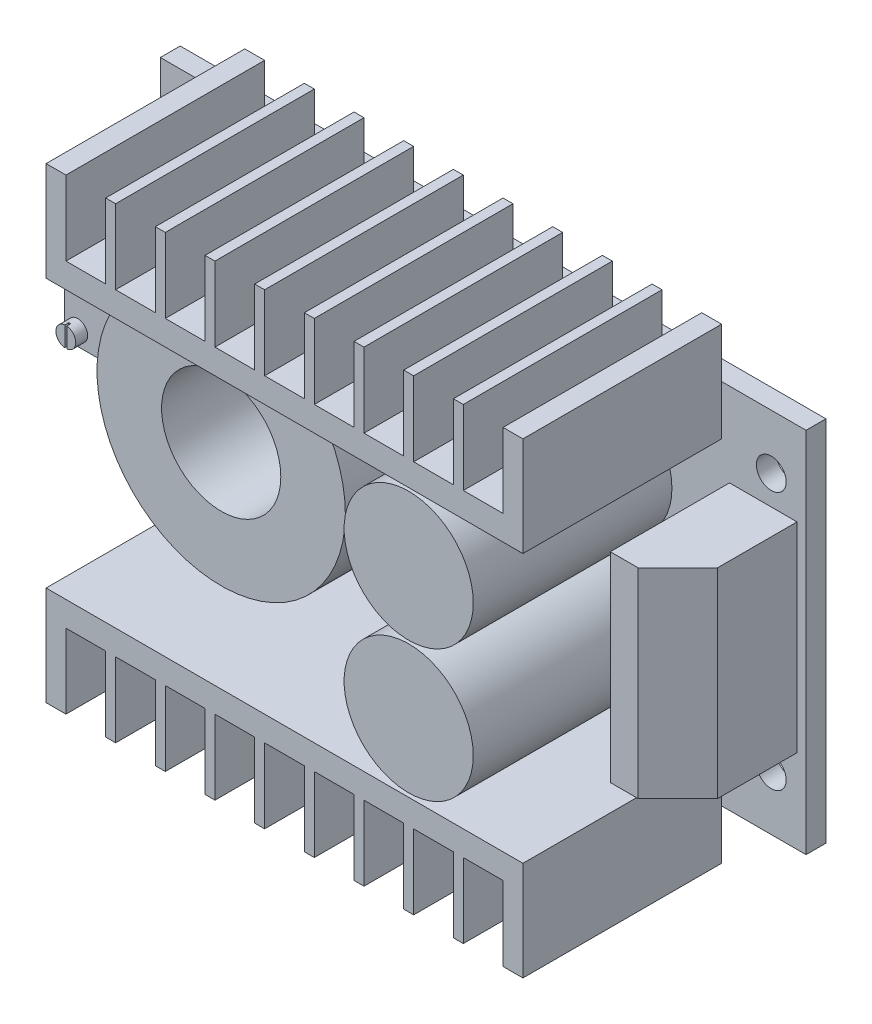
SolidWorks part; units mm, degrees
ref_plane "Front" through (0, 0, 0) normal (0, 0, 1) x (1, 0, 0)
ref_plane "Top" through (0, 0, 0) normal (0, 1, 0) x (1, 0, 0)
ref_plane "Right" through (0, 0, 0) normal (1, 0, 0) x (0, 0, -1)
sketch "Эскиз1" plane through (0, 0, 0) normal (0, 0, 1) x (1, 0, 0)
  line L1 (-32.5, 18.5) -> (32.5, 18.5)
  line L2 (-32.5, 18.5) -> (-32.5, -18.5)
  line L3 (-32.5, -18.5) -> (32.5, -18.5)
  line L4 (32.5, 18.5) -> (32.5, -18.5)
  line L5 (0, -18.5) -> (0, 18.5) construction
  line L6 (-32.5, 0) -> (32.5, 0) construction
  point P0 (0, 0)
  dimension "D1" = 37
  dimension "D2" = 65
extrude "Бобышка-Вытянуть1" add sketch "Эскиз1" along normal blind 2
sketch "Эскиз2" plane through (0, 0, 2) normal (0, 0, 1) x (1, 0, 0)
  line L0 (32.5, 18.5) -> (-32.5, 18.5) construction
  line L1 (-24, 23.5) -> (24, 23.5) construction
  line L2 (-24, 23.5) -> (-24, 13.5)
  line L3 (-24, 13.5) -> (24, 13.5)
  line L4 (24, 23.5) -> (24, 13.5)
  line L5 (0, 13.5) -> (0, 23.5) construction
  line L6 (-24, 18.5) -> (24, 18.5) construction
  line L7 (-22, 23.5) -> (-24, 23.5)
  line L8 (-2, 16) -> (2, 16)
  line L9 (-2, 16) -> (-2, 23.5)
  line L11 (2, 16) -> (2, 23.5)
  line L12 (0, 23.5) -> (0, 16) construction
  line L13 (-2, 19.75) -> (2, 19.75) construction
  line L14 (-3, 23.5) -> (-2, 23.5)
  line L15 (-3, 16) -> (-3, 23.5)
  line L16 (-7, 16) -> (-3, 16)
  line L17 (-7, 16) -> (-7, 23.5)
  line L18 (-8, 23.5) -> (-7, 23.5)
  line L19 (-8, 16) -> (-8, 23.5)
  line L20 (-12, 16) -> (-8, 16)
  line L21 (-12, 16) -> (-12, 23.5)
  line L22 (-13, 23.5) -> (-12, 23.5)
  line L23 (-13, 16) -> (-13, 23.5)
  line L24 (-17, 16) -> (-13, 16)
  line L25 (-17, 16) -> (-17, 23.5)
  line L26 (-18, 23.5) -> (-17, 23.5)
  line L27 (-18, 16) -> (-18, 23.5)
  line L28 (-22, 16) -> (-18, 16)
  line L29 (-22, 16) -> (-22, 23.5)
  line L30 (2, 23.5) -> (3, 23.5)
  line L31 (3, 16) -> (3, 23.5)
  line L32 (3, 16) -> (7, 16)
  line L33 (7, 16) -> (7, 23.5)
  line L34 (7, 23.5) -> (8, 23.5)
  line L35 (8, 16) -> (8, 23.5)
  line L36 (8, 16) -> (12, 16)
  line L37 (12, 16) -> (12, 23.5)
  line L38 (12, 23.5) -> (13, 23.5)
  line L39 (13, 16) -> (13, 23.5)
  line L40 (13, 16) -> (17, 16)
  line L41 (17, 16) -> (17, 23.5)
  line L42 (17, 23.5) -> (18, 23.5)
  line L43 (18, 16) -> (18, 23.5)
  line L44 (18, 16) -> (22, 16)
  line L45 (22, 16) -> (22, 23.5)
  line L46 (22, 23.5) -> (24, 23.5)
  line L47 (-32.5, 0) -> (32.5, 0) construction
  line L48 (-32.5, 18.5) -> (-32.5, -18.5) construction
  line L49 (32.5, -18.5) -> (32.5, 18.5) construction
  line L50 (-2, -19.75) -> (2, -19.75) construction
  line L51 (0, -23.5) -> (0, -16) construction
  line L52 (-24, -18.5) -> (24, -18.5) construction
  line L53 (0, -13.5) -> (0, -23.5) construction
  line L54 (-24, -23.5) -> (24, -23.5) construction
  line L55 (22, -23.5) -> (24, -23.5)
  line L56 (22, -16) -> (22, -23.5)
  line L57 (18, -16) -> (22, -16)
  line L58 (18, -16) -> (18, -23.5)
  line L59 (17, -23.5) -> (18, -23.5)
  line L60 (17, -16) -> (17, -23.5)
  line L61 (13, -16) -> (17, -16)
  line L62 (13, -16) -> (13, -23.5)
  line L63 (12, -23.5) -> (13, -23.5)
  line L64 (12, -16) -> (12, -23.5)
  line L65 (8, -16) -> (12, -16)
  line L66 (8, -16) -> (8, -23.5)
  line L67 (7, -23.5) -> (8, -23.5)
  line L68 (7, -16) -> (7, -23.5)
  line L69 (3, -16) -> (7, -16)
  line L70 (3, -16) -> (3, -23.5)
  line L71 (2, -23.5) -> (3, -23.5)
  line L72 (-22, -16) -> (-22, -23.5)
  line L73 (-22, -16) -> (-18, -16)
  line L74 (-18, -16) -> (-18, -23.5)
  line L75 (-18, -23.5) -> (-17, -23.5)
  line L76 (-17, -16) -> (-17, -23.5)
  line L77 (-17, -16) -> (-13, -16)
  line L78 (-13, -16) -> (-13, -23.5)
  line L79 (-13, -23.5) -> (-12, -23.5)
  line L80 (-12, -16) -> (-12, -23.5)
  line L81 (-12, -16) -> (-8, -16)
  line L82 (-8, -16) -> (-8, -23.5)
  line L83 (-8, -23.5) -> (-7, -23.5)
  line L84 (-7, -16) -> (-7, -23.5)
  line L85 (-7, -16) -> (-3, -16)
  line L86 (-3, -16) -> (-3, -23.5)
  line L87 (-3, -23.5) -> (-2, -23.5)
  line L88 (2, -16) -> (2, -23.5)
  line L89 (-2, -16) -> (-2, -23.5)
  line L90 (-2, -16) -> (2, -16)
  line L91 (-22, -23.5) -> (-24, -23.5)
  line L92 (24, -23.5) -> (24, -13.5)
  line L93 (-24, -13.5) -> (24, -13.5)
  line L94 (-24, -23.5) -> (-24, -13.5)
  point P0 (0, 18.5)
  point P6 (0, 19.75)
  point P103 (0, -19.75)
  point P104 (0, -18.5)
  dimension "D1" = 10
  dimension "D2" = 48
  dimension "D3" = 7.5
  dimension "D4" = 4
  dimension "D5" = 5
  dimension "D6" = 5
extrude "Бобышка-Вытянуть2" add sketch "Эскиз2" along normal blind 20
sketch "Эскиз3" plane through (0, 0, 2) normal (0, 0, 1) x (1, 0, 0)
  line L0 (12.5, 23.5) -> (12.5, -23.5) construction
  line L1 (13, 23.5) -> (12, 23.5) construction
  line L2 (12, -23.5) -> (13, -23.5) construction
  circle A0 centre (12.5, 6.6916) radius 6.5
  circle A1 centre (12.5, -6.6124) radius 6.5
  dimension "D1" = 13
  dimension "D2" = 13
extrude "Бобышка-Вытянуть3" add sketch "Эскиз3" along normal blind 20
sketch "Эскиз4" plane through (0, 0, 2) normal (0, 0, 1) x (1, 0, 0)
  circle A0 centre (-14.3735, 0) radius 12.5
  circle A1 centre (-14.3735, 0) radius 6
  dimension "D1" = 25
  dimension "D2" = 12
extrude "Бобышка-Вытянуть4" add sketch "Эскиз4" along normal blind 12
sketch "Эскиз5" plane through (0, 0, 2) normal (0, 0, 1) x (1, 0, 0)
  line L1 (-32.1494, 9.1427) -> (-27.1494, 9.1427)
  line L2 (-32.1494, 9.1427) -> (-32.1494, -0.8573)
  line L3 (-32.1494, -0.8573) -> (-27.1494, -0.8573)
  line L4 (-27.1494, 9.1427) -> (-27.1494, -0.8573)
  line L5 (-29.6494, -0.8573) -> (-29.6494, 9.1427) construction
  line L6 (-32.1494, 4.1427) -> (-27.1494, 4.1427) construction
  point P0 (-29.6494, 4.1427)
  dimension "D1" = 10
  dimension "D2" = 5
extrude "Бобышка-Вытянуть5" add sketch "Эскиз5" along normal blind 10
sketch "Эскиз6" plane through (0, 0, 12) normal (0, 0, 1) x (1, 0, 0)
  circle A0 centre (-30.8135, 0.582) radius 1
  dimension "D1" = 2
extrude "Бобышка-Вытянуть6" add sketch "Эскиз6" along normal blind 1.2
sketch "Эскиз7" plane through (0, 0, 2) normal (0, 0, 1) x (1, 0, 0)
  line L1 (24.796, 10.0615) -> (31.5947, 10.0615)
  line L2 (24.796, 10.0615) -> (24.796, -10.0615)
  line L3 (24.796, -10.0615) -> (31.5947, -10.0615)
  line L4 (31.5947, 10.0615) -> (31.5947, -10.0615)
  line L5 (28.1954, -10.0615) -> (28.1954, 10.0615) construction
  line L6 (24.796, 0) -> (31.5947, 0) construction
  point P0 (28.1954, 0)
  dimension "D1" = 20.1231
  dimension "D2" = 6.7987
extrude "Бобышка-Вытянуть7" add sketch "Эскиз7" along normal blind 12
chamfer "Фаска1" distance 4 angle 45 1 edges at (31.5947, 0, 14)
sketch "Эскиз8" plane through (0, 0, 2) normal (0, 0, 1) x (1, 0, 0)
  line L1 (-29, 13) -> (29, 13) construction
  line L2 (-29, 13) -> (-29, -13) construction
  line L3 (-29, -13) -> (29, -13) construction
  line L4 (29, 13) -> (29, -13) construction
  line L5 (0, -13) -> (0, 13) construction
  line L6 (-29, 0) -> (29, 0) construction
  circle A0 centre (-29, 13) radius 1.5
  circle A1 centre (29, 13) radius 1.5
  circle A2 centre (29, -13) radius 1.5
  circle A3 centre (-29, -13) radius 1.5
  point P0 (0, 0)
  dimension "D3" = 3
  dimension "D4" = 3
  dimension "D5" = 3
  dimension "D6" = 3
  dimension "D1" = 26
  dimension "D2" = 58
extrude "Вырез-Вытянуть1" cut sketch "Эскиз8" against normal through all
sketch "Sketch1" plane through (0, 0, 13.2) normal (0, 0, 1) x (1, 0, 0)
  line L1 (-30.9135, 1.6192) -> (-30.7135, 1.6192)
  line L2 (-30.9135, 1.6192) -> (-30.9135, -0.6078)
  line L3 (-30.9135, -0.6078) -> (-30.7135, -0.6078)
  line L4 (-30.7135, 1.6192) -> (-30.7135, -0.6078)
  line L5 (-30.9135, 1.6192) -> (-30.7135, -0.6078) construction
  line L6 (-30.9135, -0.6078) -> (-30.7135, 1.6192) construction
  circle A0 centre (-30.8135, 0.582) radius 1 construction
  point P4 (-30.8135, 0.5057)
  dimension "D1" = 0.2
  dimension "D2" = 0.1
extrude "Cut-Extrude1" cut sketch "Sketch1" against normal blind 0.4
